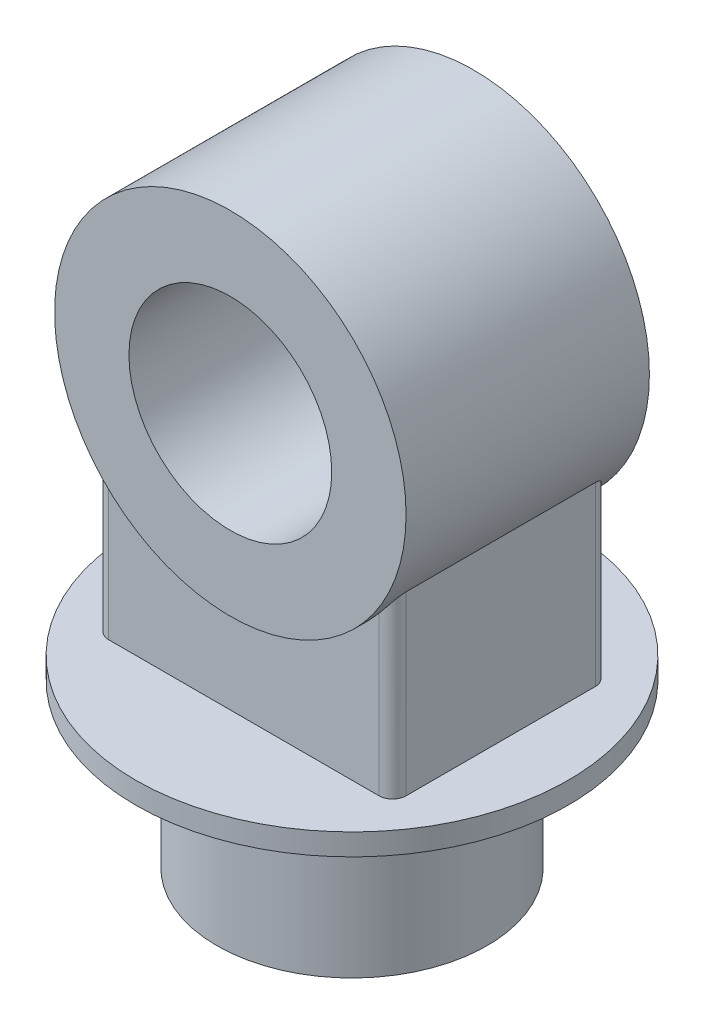
SolidWorks part; units mm, degrees
ref_plane "Ön Düzlem" through (0, 0, 0) normal (0, 0, 1) x (1, 0, 0)
ref_plane "Üst Düzlem" through (0, 0, 0) normal (0, 1, 0) x (1, 0, 0)
ref_plane "Sağ Düzlem" through (0, 0, 0) normal (1, 0, 0) x (0, 0, -1)
sketch "Çizim1" plane through (0, 0, 0) normal (0, 1, 0) x (1, 0, 0)
  circle A0 centre (0, 0) radius 100
  dimension "D1" = 200
extrude "Yükseklik-Ekstrüzyon1" add sketch "Çizim1" along normal blind 120
sketch "Çizim2" plane through (0, 120, 0) normal (0, 1, 0) x (1, 0, 0)
  circle A0 centre (0, 0) radius 160
  dimension "D1" = 320
extrude "Yükseklik-Ekstrüzyon2" add sketch "Çizim2" along normal blind 16
sketch "Çizim3" plane through (0, 0, 0) normal (0, 0, 1) x (1, 0, 0)
  line L0 (160, 136) -> (-160, 136) construction
  circle A0 centre (0, 336) radius 75
  circle A1 centre (0, 336) radius 1
  circle A2 centre (0, 336) radius 130
  dimension "D1" = 150
  dimension "D2" = 260
  dimension "D3" = 200
extrude "Yükseklik-Ekstrüzyon3" add sketch "Çizim3" along normal mid plane 180 separate body contours A2 A0
sketch "Çizim5" plane through (0, 136, 0) normal (0, 1, 0) x (1, 0, 0)
  line L1 (-110, 80) -> (110, 80)
  line L2 (-110, 80) -> (-110, -80)
  line L3 (-110, -80) -> (110, -80)
  line L4 (110, 80) -> (110, -80)
  line L5 (-110, 80) -> (110, -80) construction
  line L6 (-110, -80) -> (110, 80) construction
  point P0 (0, 0)
  dimension "D1" = 160
  dimension "D2" = 220
extrude "Yükseklik-Ekstrüzyon4" add sketch "Çizim5" along normal up to next
fillet "Radyus1" radius 10 4 edges at (110, 201.359, -80) (110, 201.359, 80) (-110, 201.359, -80) (-110, 201.359, 80)
